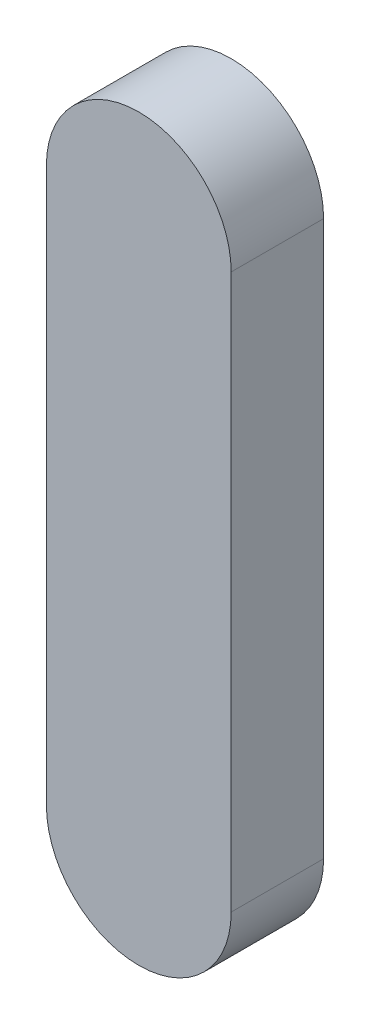
SolidWorks part; units mm, degrees
ref_plane "前视基准面" through (0, 0, 0) normal (0, 0, 1) x (1, 0, 0)
ref_plane "上视基准面" through (0, 0, 0) normal (0, 1, 0) x (1, 0, 0)
ref_plane "右视基准面" through (0, 0, 0) normal (1, 0, 0) x (0, 0, -1)
sketch "草图1" plane through (0, 0, 0) normal (0, 0, 1) x (1, 0, 0)
  line L0 (0, 0) -> (0, -30) construction
  line L1 (5, 0) -> (5, -30)
  line L2 (-5, 0) -> (-5, -30)
  arc A0 (5, 0) -> (-5, 0) centre (0, 0) ccw
  arc A1 (-5, -30) -> (5, -30) centre (0, -30) ccw
  point P3 (0, -15)
extrude "凸台-拉伸1" add sketch "草图1" along normal blind 5
